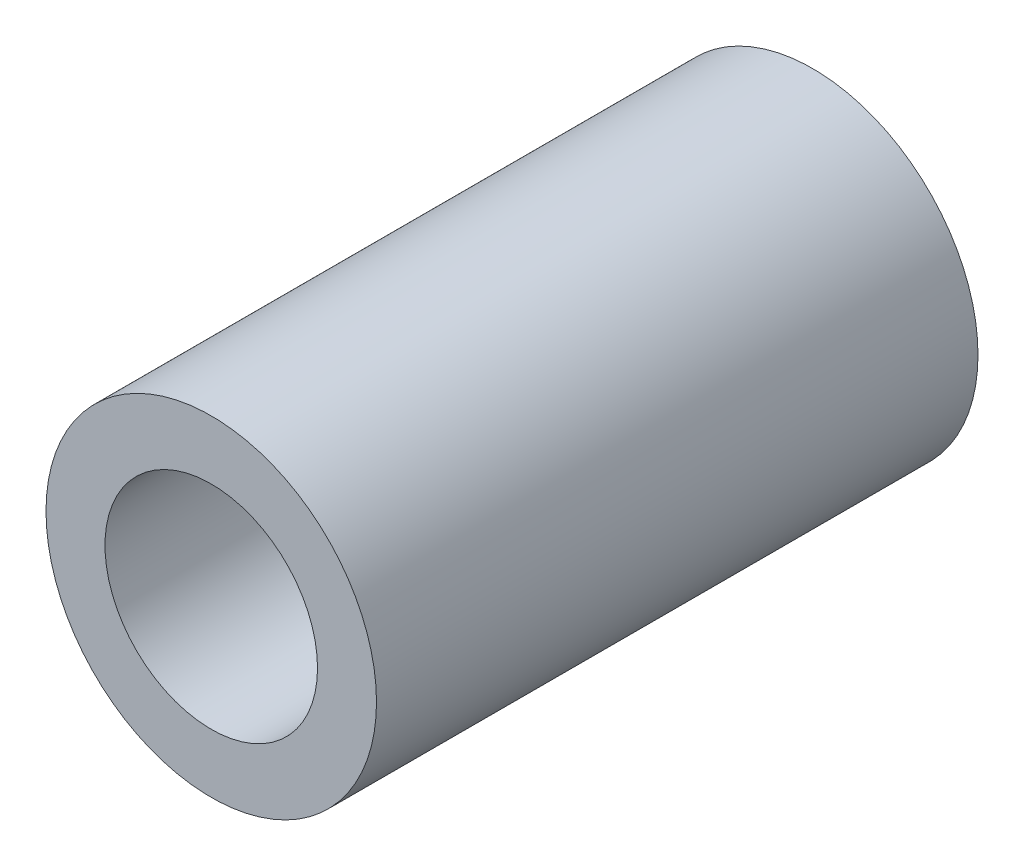
SolidWorks part; units mm, degrees
material "KNSU"
ref_plane "Alzado" through (0, 0, 0) normal (0, 0, 1) x (1, 0, 0)
ref_plane "Planta" through (0, 0, 0) normal (0, 1, 0) x (1, 0, 0)
ref_plane "Vista lateral" through (0, 0, 0) normal (1, 0, 0) x (0, 0, -1)
sketch "Croquis1" plane through (0, 0, 0) normal (0, 0, 1) x (1, 0, 0)
  circle A0 centre (0, 0) radius 15.55
  circle A1 centre (0, 0) radius 10
  dimension "D1" = 31.1
  dimension "D2" = 20
extrude "Saliente-Extruir1" add sketch "Croquis1" along normal blind 56.6
equation "\"DouterGrain\"=31.1"
equation "\"D1@Croquis1\"=\"DouterGrain\""
equation "\"DinnerGrain\"=20"
equation "\"D2@Croquis1\"=\"DinnerGrain\""
equation "\"LengthGrain\"=56.6"
equation "\"D1@Saliente-Extruir1\"=\"LengthGrain\""
